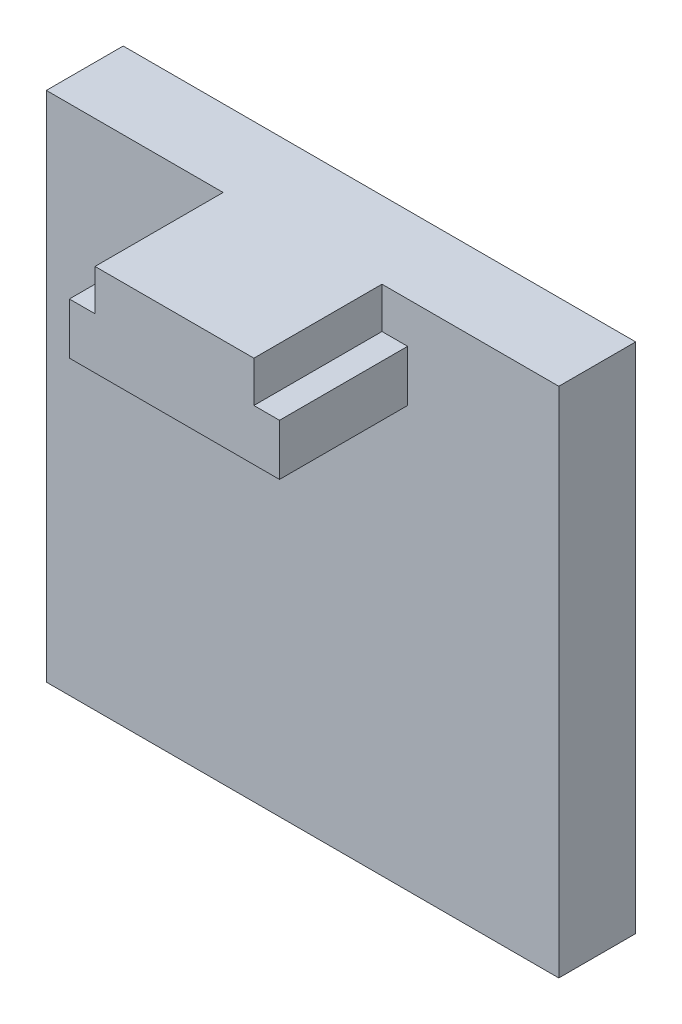
SolidWorks part; units mm, degrees
ref_plane "Front Plane" through (0, 0, 0) normal (0, 0, 1) x (1, 0, 0)
ref_plane "Top Plane" through (0, 0, 0) normal (0, 1, 0) x (1, 0, 0)
ref_plane "Right Plane" through (0, 0, 0) normal (1, 0, 0) x (0, 0, -1)
sketch "Sketch1" plane through (0, 0, 0) normal (0, 0, 1) x (1, 0, 0)
  line L1 (0, 0) -> (20, 0)
  line L2 (0, 0) -> (0, 20)
  line L3 (0, 20) -> (20, 20)
  line L4 (20, 0) -> (20, 20)
  point P6 (0, 0)
extrude "Boss-Extrude1" add sketch "Sketch1" along normal blind 3
sketch "Sketch2" plane through (0, 0, 3) normal (0, 0, 1) x (1, 0, 0)
  line L0 (6.9, 20) -> (6.9, 18.4)
  line L1 (20, 20) -> (0, 20) construction
  line L2 (6.9, 20) -> (13.1, 20)
  line L3 (6.9, 18.4) -> (5.9, 18.4)
  line L4 (5.9, 18.4) -> (5.9, 16.4)
  line L5 (5.9, 16.4) -> (13.1, 16.4)
  line L6 (13.1, 16.4) -> (14.1, 16.4)
  line L7 (14.1, 16.4) -> (14.1, 18.4)
  line L8 (14.1, 18.4) -> (13.1, 18.4)
  line L9 (13.1, 18.4) -> (13.1, 20)
extrude "Boss-Extrude2" add sketch "Sketch2" along normal blind 5
